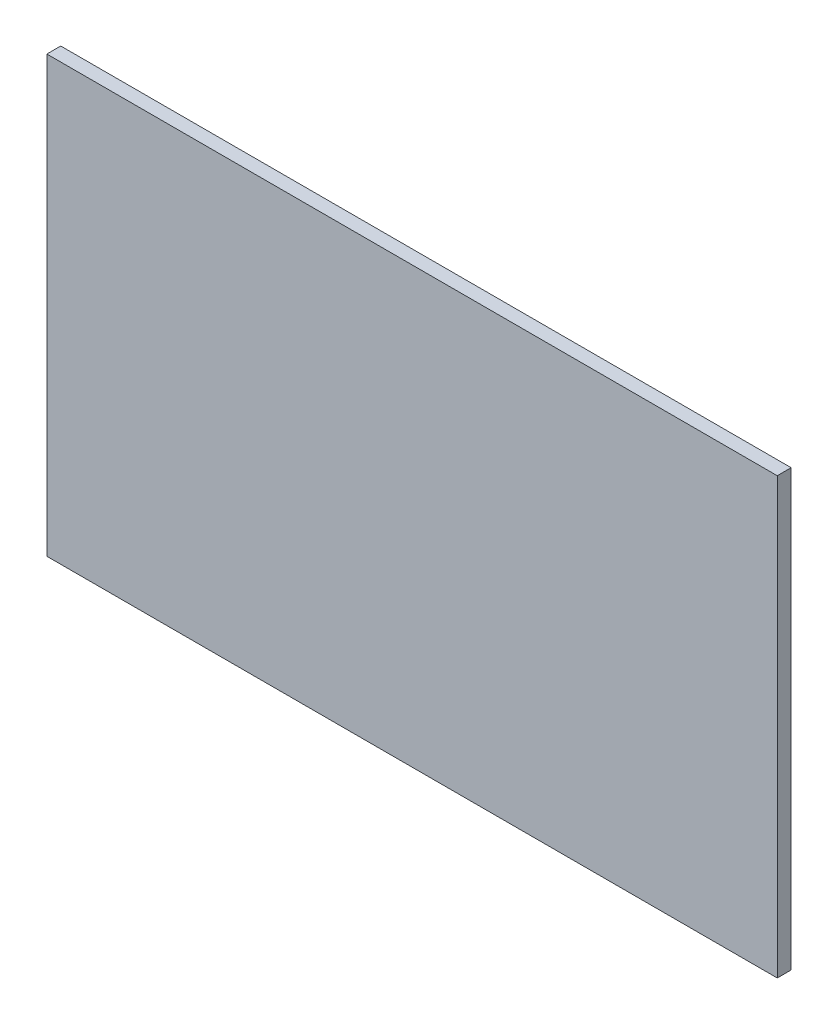
SolidWorks part; units mm, degrees
ref_plane "Front Plane" through (0, 0, 0) normal (0, 0, 1) x (1, 0, 0)
ref_plane "Top Plane" through (0, 0, 0) normal (0, 1, 0) x (1, 0, 0)
ref_plane "Right Plane" through (0, 0, 0) normal (1, 0, 0) x (0, 0, -1)
sketch "Sketch1" plane through (0, 0, 0) normal (0, 0, 1) x (1, 0, 0)
  line L1 (473.5, -282) -> (-473.5, -282)
  line L2 (473.5, -282) -> (473.5, 282)
  line L3 (473.5, 282) -> (-473.5, 282)
  line L4 (-473.5, -282) -> (-473.5, 282)
  line L5 (473.5, -282) -> (-473.5, 282) construction
  line L6 (473.5, 282) -> (-473.5, -282) construction
  point P0 (0, 0)
  dimension "D1" = 564
  dimension "D2" = 947
extrude "Boss-Extrude1" add sketch "Sketch1" along normal blind 18
equation "\"H_DSP\"=18"
equation "\"D1@Boss-Extrude1\"=\"H_DSP\""
